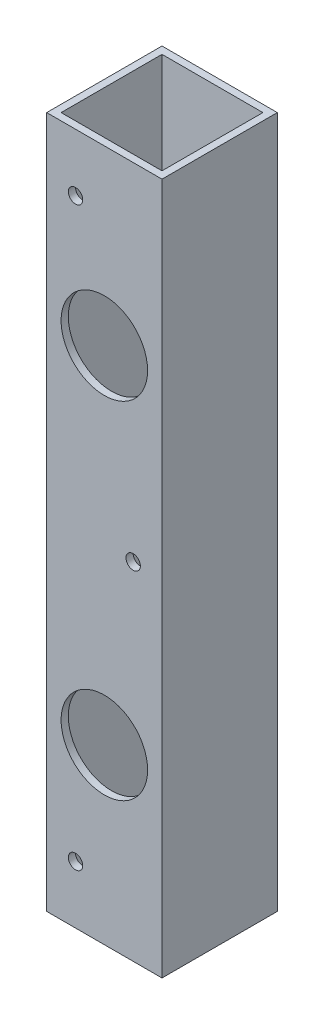
SolidWorks part; units mm, degrees
ref_plane "Front Plane" through (0, 0, 0) normal (0, 0, 1) x (1, 0, 0)
ref_plane "Top Plane" through (0, 0, 0) normal (0, 1, 0) x (1, 0, 0)
ref_plane "Right Plane" through (0, 0, 0) normal (1, 0, 0) x (0, 0, -1)
sketch "Sketch1" plane through (0, 0, 0) normal (0, 1, 0) x (1, 0, 0)
  line L1 (12.7, -12.7) -> (-12.7, -12.7)
  line L2 (12.7, -12.7) -> (12.7, 12.7)
  line L3 (12.7, 12.7) -> (-12.7, 12.7)
  line L4 (-12.7, -12.7) -> (-12.7, 12.7)
  line L5 (12.7, -12.7) -> (-12.7, 12.7) construction
  line L6 (12.7, 12.7) -> (-12.7, -12.7) construction
  point P0 (0, 0)
  dimension "D1" = 25.4
extrude "Extrude-Thin1" add sketch "Sketch1" along normal blind 152.4 thin
sketch "Sketch2" plane through (0, 0, 12.7) normal (0, 0, 1) x (1, 0, 0)
  line L0 (-12.7, 0) -> (12.7, 0) construction
  line L1 (-6.35, 139.7) -> (6.35, 76.2) construction
  line L2 (6.35, 76.2) -> (-6.35, 12.7) construction
  line L6 (-12.7, 152.4) -> (-12.7, 0) construction
  line L7 (-12.7, 152.4) -> (12.7, 152.4) construction
  line L8 (12.7, 152.4) -> (12.7, 0) construction
  circle A0 centre (0, 114.3) radius 9.525
  circle A1 centre (0, 38.1) radius 9.525
  circle A7 centre (-6.35, 139.7) radius 1.5875
  circle A8 centre (6.35, 76.2) radius 1.5875
  circle A9 centre (-6.35, 12.7) radius 1.5875
  dimension "D1" = 19.05
  dimension "D2" = 38.1
  dimension "D3" = 114.3
  dimension "D4" = 3.175
  dimension "D5" = 6.35
  dimension "D6" = 12.7
  dimension "D7" = 6.35
  dimension "D8" = 12.7
extrude "Cut-Extrude1" cut sketch "Sketch2" against normal up to next
sketch "Sketch4" plane through (0, 0, -11.1125) normal (0, 0, 1) x (1, 0, 0)
  circle A0 centre (0, 114.3) radius 3.3782
  circle A1 centre (0, 38.1) radius 3.3782
  dimension "D1" = 6.7564
extrude "Cut-Extrude2" cut sketch "Sketch4" against normal through all
